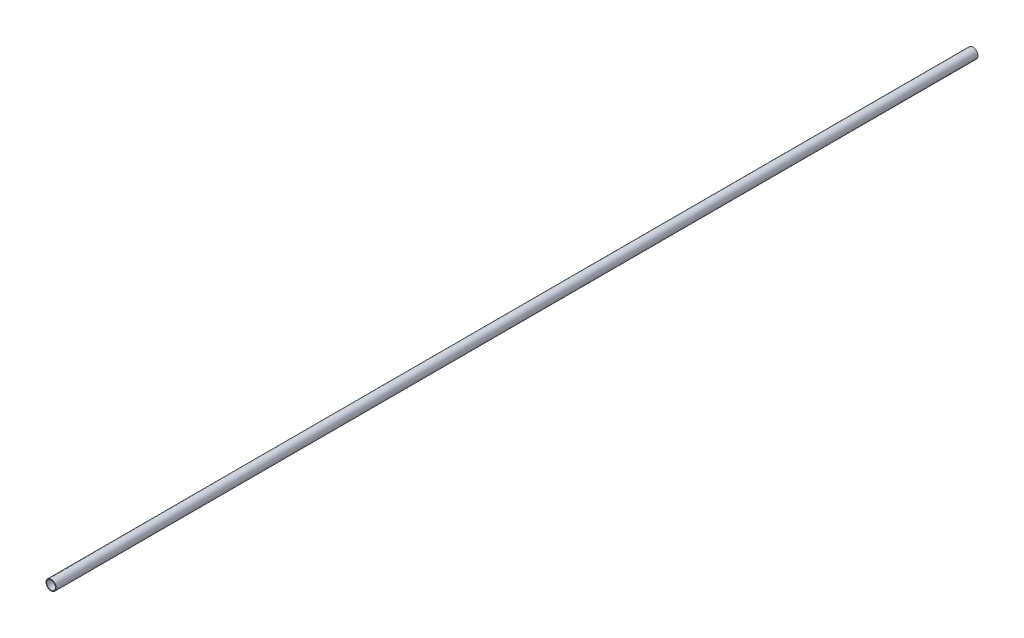
SolidWorks part; units mm, degrees
ref_plane "Front" through (0, 0, 0) normal (0, 0, 1) x (1, 0, 0)
ref_plane "Top" through (0, 0, 0) normal (0, 1, 0) x (1, 0, 0)
ref_plane "Side" through (0, 0, 0) normal (1, 0, 0) x (0, 0, -1)
sketch "PipeSketch" plane through (0, 0, 0) normal (0, 0, 1) x (1, 0, 0)
  circle A0 centre (0, 0) radius 30.226
  circle A1 centre (0, 0) radius 26.3144
  dimension "OuterDiameter" = 60.452
  dimension "InnerDiameter" = 52.6288
extrude "Extrusion" add sketch "PipeSketch" along normal blind 5486.4
sketch "FilterSketch" plane through (0, 0, 0) normal (0, 0, 1) x (1, 0, 0)
  circle A0 centre (0, 0) radius 25.4 construction
  dimension "NominalDiameter" = 50.8
